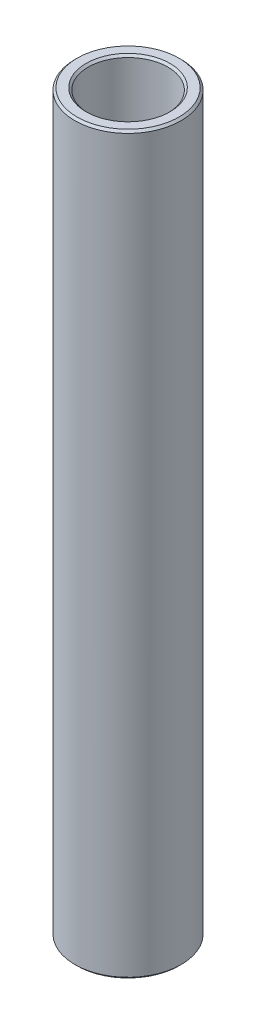
SolidWorks part; units mm, degrees
ref_plane "Front Plane" through (0, 0, 0) normal (0, 0, 1) x (1, 0, 0)
ref_plane "Top Plane" through (0, 0, 0) normal (0, 1, 0) x (1, 0, 0)
ref_plane "Right Plane" through (0, 0, 0) normal (1, 0, 0) x (0, 0, -1)
sketch "Sketch1" plane through (0, 0, 0) normal (0, 0, 1) x (1, 0, 0)
  line L0 (4.7625, 131.7624) -> (4.7625, 219.6274)
  line L1 (4.7625, 219.6274) -> (6.35, 219.6274)
  line L2 (6.35, 219.6274) -> (6.35, 131.7624)
  line L3 (6.35, 131.7624) -> (4.7625, 131.7624)
  line L4 (120.0875, 140.4936) -> (10.0875, 140.4936) construction
  line L6 (0, 122.2374) -> (0, 229.1524) construction
  dimension "D1" = 9.525
  dimension "D2" = 9.525
  dimension "D3" = 12.7
  dimension "D4" = 9.525
revolve "Revolve1" add sketch "Sketch1" angle 360 about L6
chamfer "Chamfer1" distance 0.254 angle 45 4 edges at (6.35, 219.6274, 0) (4.7625, 219.6274, 0) (4.7625, 131.7624, 0) (6.35, 131.7624, 0)
equation "\"D4@Sketch1\"=\"D1@Sketch1\""
